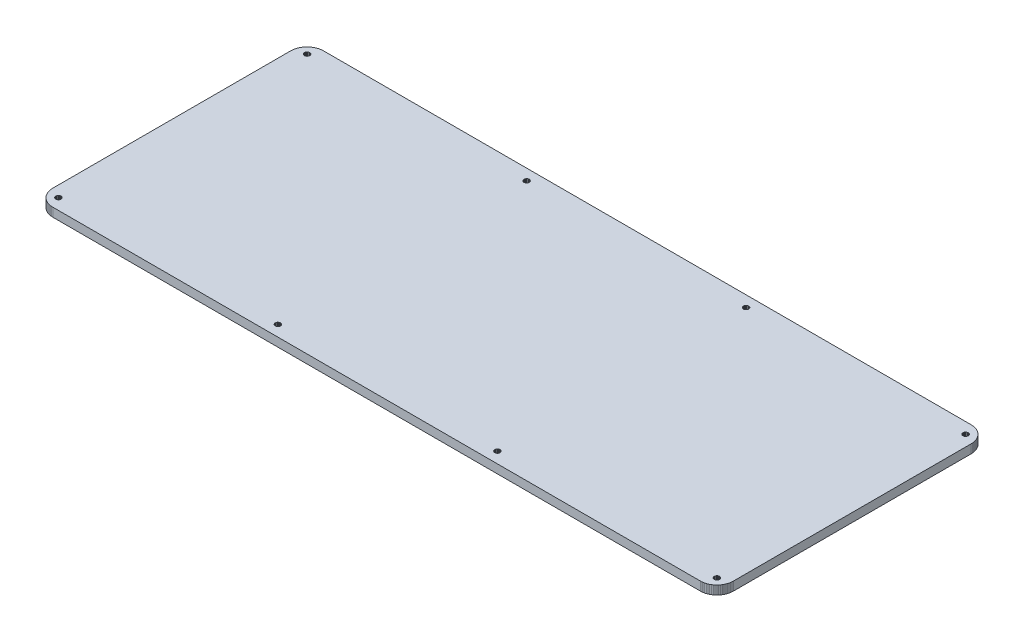
SolidWorks part; units mm, degrees
material "Acrylic (Medium-high impact)"
ref_plane "Front Plane" through (0, 0, 0) normal (0, 0, 1) x (1, 0, 0)
ref_plane "Top Plane" through (0, 0, 0) normal (0, 1, 0) x (1, 0, 0)
ref_plane "Right Plane" through (0, 0, 0) normal (1, 0, 0) x (0, 0, -1)
sketch "Sketch1" plane through (0, 0, 0) normal (0, 1, 0) x (1, 0, 0)
  line L0 (362.807, 147.967) -> (363.513, 147.941)
  line L1 (363.513, 147.941) -> (364.215, 147.857)
  line L2 (364.215, 147.857) -> (364.91, 147.719)
  line L3 (364.91, 147.719) -> (365.591, 147.527)
  line L4 (365.591, 147.527) -> (366.254, 147.282)
  line L5 (366.254, 147.282) -> (366.896, 146.987)
  line L6 (366.896, 146.987) -> (367.51, 146.641)
  line L7 (367.51, 146.641) -> (368.099, 146.25)
  line L8 (368.099, 146.25) -> (368.653, 145.812)
  line L9 (368.653, 145.812) -> (369.171, 145.331)
  line L10 (369.171, 145.331) -> (369.651, 144.812)
  line L11 (369.651, 144.812) -> (370.089, 144.259)
  line L12 (370.089, 144.259) -> (370.48, 143.67)
  line L13 (370.48, 143.67) -> (370.826, 143.053)
  line L14 (370.826, 143.053) -> (371.122, 142.412)
  line L15 (371.122, 142.412) -> (371.369, 141.749)
  line L16 (371.369, 141.749) -> (371.56, 141.07)
  line L17 (371.56, 141.07) -> (371.697, 140.375)
  line L18 (371.697, 140.375) -> (371.778, 139.674)
  line L19 (371.778, 139.674) -> (371.807, 138.967)
  line L20 (371.807, 138.967) -> (371.807, 9.0909)
  line L21 (371.807, 9.0909) -> (371.778, 8.3854)
  line L22 (371.778, 8.3854) -> (371.697, 7.684)
  line L23 (371.697, 7.684) -> (371.56, 6.9908)
  line L24 (371.56, 6.9908) -> (371.369, 6.31)
  line L25 (371.369, 6.31) -> (371.122, 5.6472)
  line L26 (371.122, 5.6472) -> (370.826, 5.0064)
  line L27 (370.826, 5.0064) -> (370.48, 4.3891)
  line L28 (370.48, 4.3891) -> (370.089, 3.8006)
  line L29 (370.089, 3.8006) -> (369.651, 3.2467)
  line L30 (369.651, 3.2467) -> (369.171, 2.7285)
  line L31 (369.171, 2.7285) -> (368.653, 2.2476)
  line L32 (368.653, 2.2476) -> (368.099, 1.8107)
  line L33 (368.099, 1.8107) -> (367.51, 1.418)
  line L34 (367.51, 1.418) -> (366.896, 1.0721)
  line L35 (366.896, 1.0721) -> (366.254, 0.7772)
  line L36 (366.254, 0.7772) -> (365.591, 0.5319)
  line L37 (365.591, 0.5319) -> (364.91, 0.3404)
  line L38 (364.91, 0.3404) -> (364.215, 0.2026)
  line L39 (364.215, 0.2026) -> (363.513, 0.1185)
  line L40 (363.513, 0.1185) -> (362.807, 0.091)
  line L41 (362.807, 0.091) -> (9.0951, 0.091)
  line L42 (9.0951, 0.091) -> (8.3881, 0.1185)
  line L43 (8.3881, 0.1185) -> (7.6867, 0.2026)
  line L44 (7.6867, 0.2026) -> (6.9922, 0.3404)
  line L45 (6.9922, 0.3404) -> (6.3128, 0.5319)
  line L46 (6.3128, 0.5319) -> (5.6499, 0.7772)
  line L47 (5.6499, 0.7772) -> (5.0092, 1.0721)
  line L48 (5.0092, 1.0721) -> (4.3918, 1.418)
  line L49 (4.3918, 1.418) -> (3.8034, 1.8107)
  line L50 (3.8034, 1.8107) -> (3.2494, 2.2476)
  line L51 (3.2494, 2.2476) -> (2.7313, 2.7285)
  line L52 (2.7313, 2.7285) -> (2.2503, 3.2467)
  line L53 (2.2503, 3.2467) -> (1.8121, 3.8006)
  line L54 (1.8121, 3.8006) -> (1.4208, 4.3891)
  line L55 (1.4208, 4.3891) -> (1.0749, 5.0064)
  line L56 (1.0749, 5.0064) -> (0.78, 5.6472)
  line L57 (0.78, 5.6472) -> (0.5347, 6.31)
  line L58 (0.5347, 6.31) -> (0.3431, 6.9908)
  line L59 (0.3431, 6.9908) -> (0.2053, 7.684)
  line L60 (0.2053, 7.684) -> (0.1213, 8.3854)
  line L61 (0.1213, 8.3854) -> (0.0937, 9.0923)
  line L62 (0.0937, 9.0923) -> (0.0951, 138.967)
  line L63 (0.0951, 138.967) -> (0.1213, 139.674)
  line L64 (0.1213, 139.674) -> (0.2053, 140.375)
  line L65 (0.2053, 140.375) -> (0.3431, 141.07)
  line L66 (0.3431, 141.07) -> (0.5347, 141.749)
  line L67 (0.5347, 141.749) -> (0.78, 142.412)
  line L68 (0.78, 142.412) -> (1.0749, 143.053)
  line L69 (1.0749, 143.053) -> (1.4208, 143.67)
  line L70 (1.4208, 143.67) -> (1.8121, 144.259)
  line L71 (1.8121, 144.259) -> (2.2503, 144.812)
  line L72 (2.2503, 144.812) -> (2.7313, 145.331)
  line L73 (2.7313, 145.331) -> (3.2494, 145.812)
  line L74 (3.2494, 145.812) -> (3.8034, 146.25)
  line L75 (3.8034, 146.25) -> (4.3918, 146.641)
  line L76 (4.3918, 146.641) -> (5.0092, 146.987)
  line L77 (5.0092, 146.987) -> (5.6499, 147.282)
  line L78 (5.6499, 147.282) -> (6.3128, 147.527)
  line L79 (6.3128, 147.527) -> (6.9922, 147.719)
  line L80 (6.9922, 147.719) -> (7.6867, 147.857)
  line L81 (7.6867, 147.857) -> (8.3881, 147.941)
  line L82 (8.3881, 147.941) -> (9.0951, 147.968)
  line L83 (9.0951, 147.968) -> (362.807, 147.967)
  line L84 (365.326, 7.5186) -> (364.917, 7.3119)
  line L85 (364.917, 7.3119) -> (364.589, 6.9825)
  line L86 (364.589, 6.9825) -> (364.381, 6.5719)
  line L87 (364.381, 6.5719) -> (364.307, 6.1157)
  line L88 (364.307, 6.1157) -> (364.381, 5.661)
  line L89 (364.381, 5.661) -> (364.589, 5.2503)
  line L90 (364.589, 5.2503) -> (364.917, 4.9237)
  line L91 (364.917, 4.9237) -> (365.326, 4.7143)
  line L92 (365.326, 4.7143) -> (365.781, 4.6413)
  line L93 (365.781, 4.6413) -> (366.24, 4.7143)
  line L94 (366.24, 4.7143) -> (366.649, 4.9237)
  line L95 (366.649, 4.9237) -> (366.977, 5.2503)
  line L96 (366.977, 5.2503) -> (367.185, 5.661)
  line L97 (367.185, 5.661) -> (367.259, 6.1157)
  line L98 (367.259, 6.1157) -> (367.185, 6.5719)
  line L99 (367.185, 6.5719) -> (366.977, 6.9825)
  line L100 (366.977, 6.9825) -> (366.649, 7.3119)
  line L101 (366.649, 7.3119) -> (366.24, 7.5186)
  line L102 (366.24, 7.5186) -> (365.781, 7.5916)
  line L103 (365.781, 7.5916) -> (365.326, 7.5186)
  line L104 (245.438, 7.5186) -> (245.027, 7.3119)
  line L105 (245.027, 7.3119) -> (244.703, 6.9825)
  line L106 (244.703, 6.9825) -> (244.492, 6.5719)
  line L107 (244.492, 6.5719) -> (244.42, 6.1157)
  line L108 (244.42, 6.1157) -> (244.492, 5.661)
  line L109 (244.492, 5.661) -> (244.703, 5.2503)
  line L110 (244.703, 5.2503) -> (245.027, 4.9237)
  line L111 (245.027, 4.9237) -> (245.438, 4.7143)
  line L112 (245.438, 4.7143) -> (245.894, 4.6413)
  line L113 (245.894, 4.6413) -> (246.35, 4.7143)
  line L114 (246.35, 4.7143) -> (246.761, 4.9237)
  line L115 (246.761, 4.9237) -> (247.088, 5.2503)
  line L116 (247.088, 5.2503) -> (247.297, 5.661)
  line L117 (247.297, 5.661) -> (247.37, 6.1157)
  line L118 (247.37, 6.1157) -> (247.297, 6.5719)
  line L119 (247.297, 6.5719) -> (247.088, 6.9825)
  line L120 (247.088, 6.9825) -> (246.761, 7.3119)
  line L121 (246.761, 7.3119) -> (246.35, 7.5186)
  line L122 (246.35, 7.5186) -> (245.894, 7.5916)
  line L123 (245.894, 7.5916) -> (245.438, 7.5186)
  line L124 (125.552, 7.5186) -> (125.138, 7.3119)
  line L125 (125.138, 7.3119) -> (124.815, 6.9825)
  line L126 (124.815, 6.9825) -> (124.604, 6.5719)
  line L127 (124.604, 6.5719) -> (124.532, 6.1157)
  line L128 (124.532, 6.1157) -> (124.604, 5.661)
  line L129 (124.604, 5.661) -> (124.815, 5.2503)
  line L130 (124.815, 5.2503) -> (125.138, 4.9237)
  line L131 (125.138, 4.9237) -> (125.552, 4.7143)
  line L132 (125.552, 4.7143) -> (126.007, 4.6413)
  line L133 (126.007, 4.6413) -> (126.463, 4.7143)
  line L134 (126.463, 4.7143) -> (126.873, 4.9237)
  line L135 (126.873, 4.9237) -> (127.201, 5.2503)
  line L136 (127.201, 5.2503) -> (127.409, 5.661)
  line L137 (127.409, 5.661) -> (127.482, 6.1157)
  line L138 (127.482, 6.1157) -> (127.409, 6.5719)
  line L139 (127.409, 6.5719) -> (127.201, 6.9825)
  line L140 (127.201, 6.9825) -> (126.873, 7.3119)
  line L141 (126.873, 7.3119) -> (126.463, 7.5186)
  line L142 (126.463, 7.5186) -> (126.007, 7.5916)
  line L143 (126.007, 7.5916) -> (125.552, 7.5186)
  line L144 (5.6637, 7.5186) -> (5.2531, 7.3119)
  line L145 (5.2531, 7.3119) -> (4.9251, 6.9825)
  line L146 (4.9251, 6.9825) -> (4.717, 6.5719)
  line L147 (4.717, 6.5719) -> (4.644, 6.1157)
  line L148 (4.644, 6.1157) -> (4.717, 5.661)
  line L149 (4.717, 5.661) -> (4.9251, 5.2503)
  line L150 (4.9251, 5.2503) -> (5.2531, 4.9237)
  line L151 (5.2531, 4.9237) -> (5.6637, 4.7143)
  line L152 (5.6637, 4.7143) -> (6.1185, 4.6413)
  line L153 (6.1185, 4.6413) -> (6.5746, 4.7143)
  line L154 (6.5746, 4.7143) -> (6.9853, 4.9237)
  line L155 (6.9853, 4.9237) -> (7.3133, 5.2503)
  line L156 (7.3133, 5.2503) -> (7.5213, 5.661)
  line L157 (7.5213, 5.661) -> (7.5944, 6.1157)
  line L158 (7.5944, 6.1157) -> (7.5213, 6.5719)
  line L159 (7.5213, 6.5719) -> (7.3133, 6.9825)
  line L160 (7.3133, 6.9825) -> (6.9853, 7.3119)
  line L161 (6.9853, 7.3119) -> (6.5746, 7.5186)
  line L162 (6.5746, 7.5186) -> (6.1185, 7.5916)
  line L163 (6.1185, 7.5916) -> (5.6637, 7.5186)
  line L164 (125.552, 143.345) -> (125.138, 143.137)
  line L165 (125.138, 143.137) -> (124.815, 142.809)
  line L166 (124.815, 142.809) -> (124.604, 142.398)
  line L167 (124.604, 142.398) -> (124.532, 141.942)
  line L168 (124.532, 141.942) -> (124.604, 141.487)
  line L169 (124.604, 141.487) -> (124.815, 141.077)
  line L170 (124.815, 141.077) -> (125.138, 140.75)
  line L171 (125.138, 140.75) -> (125.552, 140.541)
  line L172 (125.552, 140.541) -> (126.007, 140.468)
  line L173 (126.007, 140.468) -> (126.463, 140.541)
  line L174 (126.463, 140.541) -> (126.873, 140.75)
  line L175 (126.873, 140.75) -> (127.201, 141.077)
  line L176 (127.201, 141.077) -> (127.409, 141.487)
  line L177 (127.409, 141.487) -> (127.482, 141.942)
  line L178 (127.482, 141.942) -> (127.409, 142.398)
  line L179 (127.409, 142.398) -> (127.201, 142.809)
  line L180 (127.201, 142.809) -> (126.873, 143.137)
  line L181 (126.873, 143.137) -> (126.463, 143.345)
  line L182 (126.463, 143.345) -> (126.007, 143.417)
  line L183 (126.007, 143.417) -> (125.552, 143.345)
  line L184 (245.438, 143.345) -> (245.027, 143.137)
  line L185 (245.027, 143.137) -> (244.703, 142.809)
  line L186 (244.703, 142.809) -> (244.492, 142.398)
  line L187 (244.492, 142.398) -> (244.42, 141.942)
  line L188 (244.42, 141.942) -> (244.492, 141.487)
  line L189 (244.492, 141.487) -> (244.703, 141.077)
  line L190 (244.703, 141.077) -> (245.027, 140.75)
  line L191 (245.027, 140.75) -> (245.438, 140.541)
  line L192 (245.438, 140.541) -> (245.894, 140.468)
  line L193 (245.894, 140.468) -> (246.35, 140.541)
  line L194 (246.35, 140.541) -> (246.761, 140.75)
  line L195 (246.761, 140.75) -> (247.088, 141.077)
  line L196 (247.088, 141.077) -> (247.297, 141.487)
  line L197 (247.297, 141.487) -> (247.37, 141.942)
  line L198 (247.37, 141.942) -> (247.297, 142.398)
  line L199 (247.297, 142.398) -> (247.088, 142.809)
  line L200 (247.088, 142.809) -> (246.761, 143.137)
  line L201 (246.761, 143.137) -> (246.35, 143.345)
  line L202 (246.35, 143.345) -> (245.894, 143.417)
  line L203 (245.894, 143.417) -> (245.438, 143.345)
  line L204 (365.326, 143.345) -> (364.917, 143.137)
  line L205 (364.917, 143.137) -> (364.589, 142.809)
  line L206 (364.589, 142.809) -> (364.381, 142.398)
  line L207 (364.381, 142.398) -> (364.307, 141.942)
  line L208 (364.307, 141.942) -> (364.381, 141.487)
  line L209 (364.381, 141.487) -> (364.589, 141.077)
  line L210 (364.589, 141.077) -> (364.917, 140.75)
  line L211 (364.917, 140.75) -> (365.326, 140.541)
  line L212 (365.326, 140.541) -> (365.781, 140.468)
  line L213 (365.781, 140.468) -> (366.24, 140.541)
  line L214 (366.24, 140.541) -> (366.649, 140.75)
  line L215 (366.649, 140.75) -> (366.977, 141.077)
  line L216 (366.977, 141.077) -> (367.185, 141.487)
  line L217 (367.185, 141.487) -> (367.259, 141.942)
  line L218 (367.259, 141.942) -> (367.185, 142.398)
  line L219 (367.185, 142.398) -> (366.977, 142.809)
  line L220 (366.977, 142.809) -> (366.649, 143.137)
  line L221 (366.649, 143.137) -> (366.24, 143.345)
  line L222 (366.24, 143.345) -> (365.781, 143.417)
  line L223 (365.781, 143.417) -> (365.326, 143.345)
  line L224 (5.6637, 143.345) -> (5.2531, 143.137)
  line L225 (5.2531, 143.137) -> (4.9251, 142.809)
  line L226 (4.9251, 142.809) -> (4.717, 142.398)
  line L227 (4.717, 142.398) -> (4.644, 141.942)
  line L228 (4.644, 141.942) -> (4.717, 141.487)
  line L229 (4.717, 141.487) -> (4.9251, 141.077)
  line L230 (4.9251, 141.077) -> (5.2531, 140.75)
  line L231 (5.2531, 140.75) -> (5.6637, 140.541)
  line L232 (5.6637, 140.541) -> (6.1185, 140.468)
  line L233 (6.1185, 140.468) -> (6.5746, 140.541)
  line L234 (6.5746, 140.541) -> (6.9853, 140.75)
  line L235 (6.9853, 140.75) -> (7.3133, 141.077)
  line L236 (7.3133, 141.077) -> (7.5213, 141.487)
  line L237 (7.5213, 141.487) -> (7.5944, 141.942)
  line L238 (7.5944, 141.942) -> (7.5213, 142.398)
  line L239 (7.5213, 142.398) -> (7.3133, 142.809)
  line L240 (7.3133, 142.809) -> (6.9853, 143.137)
  line L241 (6.9853, 143.137) -> (6.5746, 143.345)
  line L242 (6.5746, 143.345) -> (6.1185, 143.417)
  line L243 (6.1185, 143.417) -> (5.6637, 143.345)
extrude "Boss-Extrude1" add sketch "Sketch1" along normal blind 4.7625
sketch "Sketch3" plane through (0, 0, 0) normal (0, -1, 0) x (1, 0, 0)
  line L0 (371.807, -74.029) -> (0.0944, -74.0296) construction
  line L1 (371.807, -9.0909) -> (371.807, -138.967) construction
  line L2 (0.0951, -138.967) -> (0.0937, -9.0923) construction
  line L3 (185.951, -147.9675) -> (185.951, -0.091) construction
  line L4 (362.807, -147.967) -> (9.0951, -147.968) construction
  line L5 (9.0951, -0.091) -> (362.807, -0.091) construction
